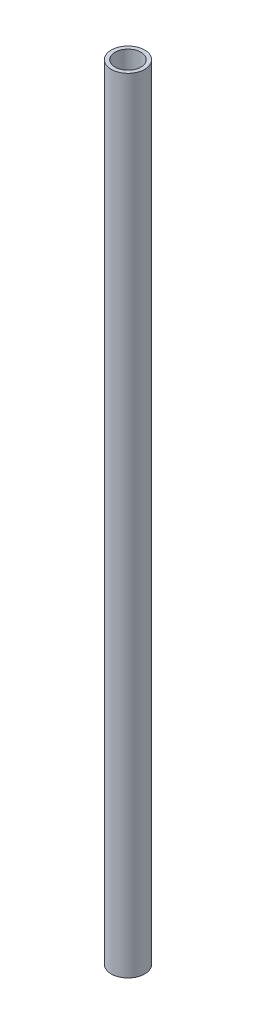
SolidWorks part; units mm, degrees
ref_plane "Front Plane" through (0, 0, 0) normal (0, 0, 1) x (1, 0, 0)
ref_plane "Top Plane" through (0, 0, 0) normal (0, 1, 0) x (1, 0, 0)
ref_plane "Right Plane" through (0, 0, 0) normal (1, 0, 0) x (0, 0, -1)
sketch "Sketch1" plane through (0, 0, 0) normal (0, 1, 0) x (1, 0, 0)
  circle A0 centre (0, 0) radius 4.6
  circle A1 centre (0, 0) radius 5.95
  dimension "D1" = 9.2
  dimension "D2" = 11.9
extrude "Boss-Extrude1" add sketch "Sketch1" along normal blind 278.5
